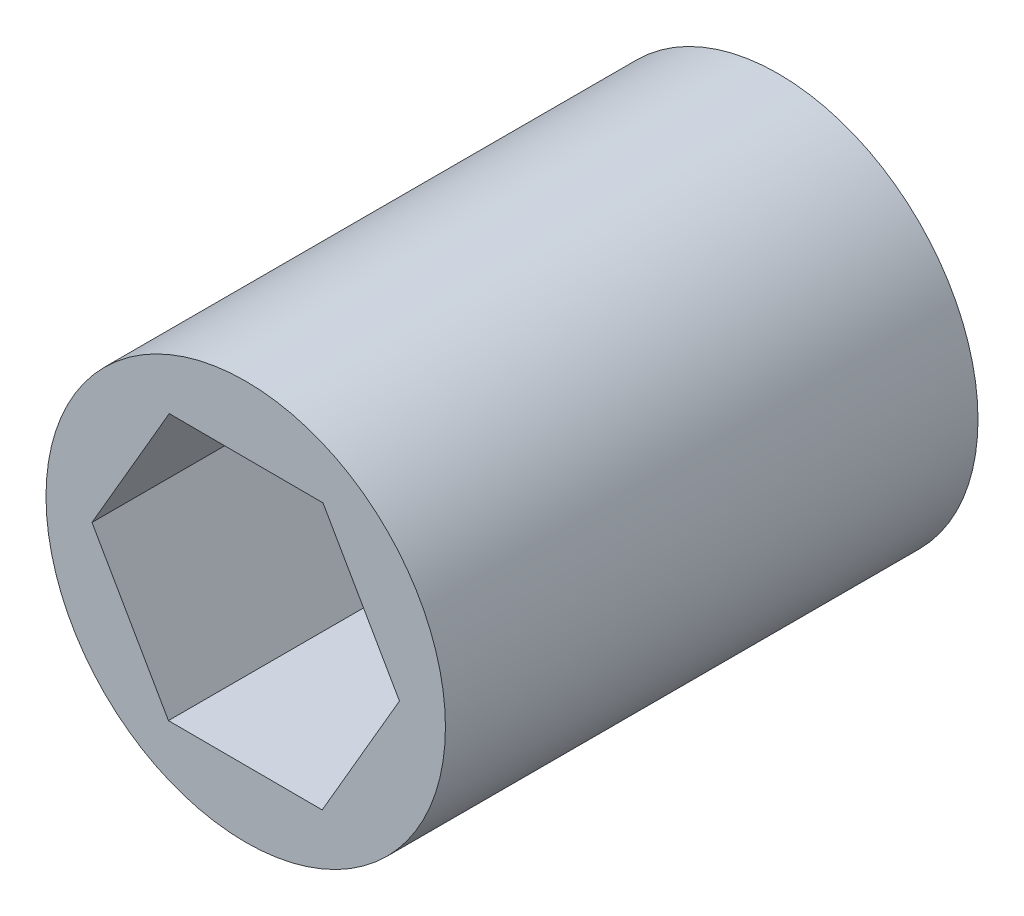
SolidWorks part; units mm, degrees
material "PET"
ref_plane "Front Plane" through (0, 0, 0) normal (0, 0, 1) x (1, 0, 0)
ref_plane "Top Plane" through (0, 0, 0) normal (0, 1, 0) x (1, 0, 0)
ref_plane "Right Plane" through (0, 0, 0) normal (1, 0, 0) x (0, 0, -1)
sketch "Sketch1" plane through (0, 0, 0) normal (0, 0, 1) x (1, 0, 0)
  line L1 (3.647, -6.361) -> (7.3323, -0.0221)
  line L2 (7.3323, -0.0221) -> (3.6853, 6.3389)
  line L3 (3.6853, 6.3389) -> (-3.647, 6.361)
  line L4 (-3.647, 6.361) -> (-7.3323, 0.0221)
  line L5 (-7.3323, 0.0221) -> (-3.6853, -6.3389)
  line L6 (-3.6853, -6.3389) -> (3.647, -6.361)
  circle A0 centre (0, 0) radius 9.525
  circle A1 centre (0, 0) radius 6.35 construction
  dimension "D1" = 19.05
  dimension "D2" = 12.7
extrude "Boss-Extrude1" add sketch "Sketch1" along normal blind 25.4
